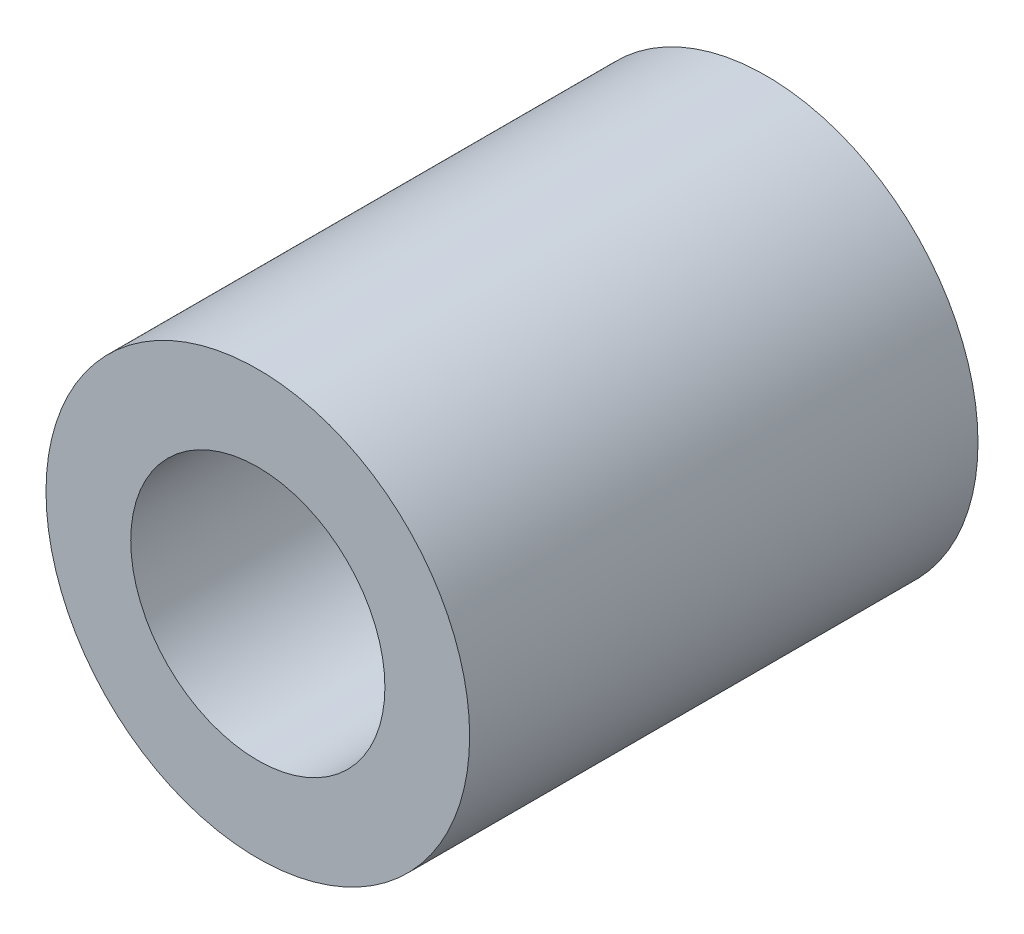
SolidWorks part; units mm, degrees
ref_plane "Plano frontal" through (0, 0, 0) normal (0, 0, 1) x (1, 0, 0)
ref_plane "Plano superior" through (0, 0, 0) normal (0, 1, 0) x (1, 0, 0)
ref_plane "Plano direito" through (0, 0, 0) normal (1, 0, 0) x (0, 0, -1)
sketch "Esboço1" plane through (0, 0, 0) normal (0, 0, 1) x (1, 0, 0)
  circle A0 centre (0, 0) radius 3
  circle A1 centre (0, 0) radius 5
  dimension "D1" = 6
  dimension "D2" = 10
extrude "Ressalto-extrusão1" add sketch "Esboço1" along normal blind 12
